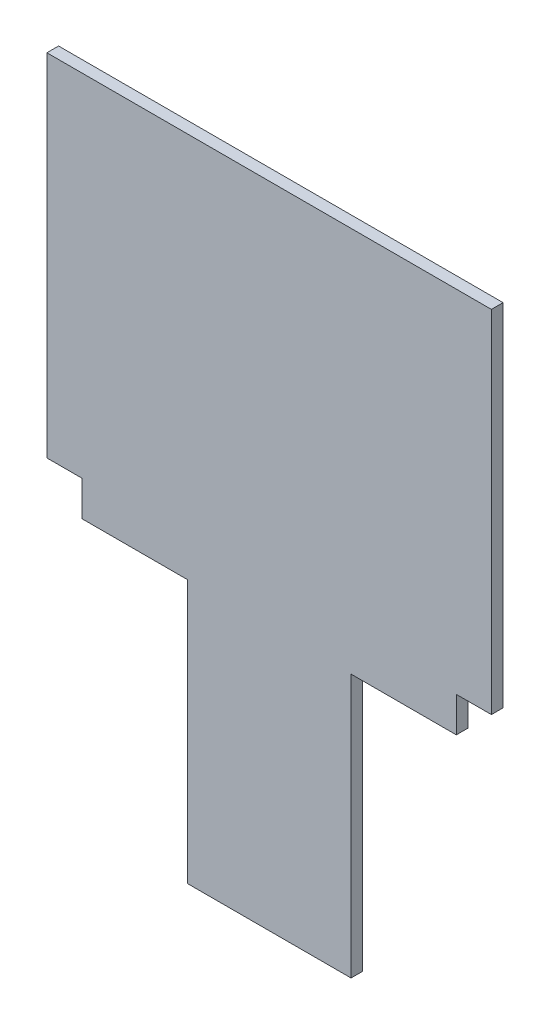
SolidWorks part; units mm, degrees
ref_plane "Ebene vorne" through (0, 0, 0) normal (0, 0, 1) x (1, 0, 0)
ref_plane "Ebene oben" through (0, 0, 0) normal (0, 1, 0) x (1, 0, 0)
ref_plane "Ebene rechts" through (0, 0, 0) normal (1, 0, 0) x (0, 0, -1)
sketch "Skizze1" plane through (0, 0, 0) normal (0, 0, 1) x (1, 0, 0)
  line L0 (14, -113) -> (14, -68) construction
  line L1 (14, -113) -> (-14, -113) construction
  line L2 (-14, -68) -> (-14, -113) construction
  line L3 (-38, -2) -> (-38, -62) construction
  line L4 (-32, -62) -> (-38, -62) construction
  line L5 (-32, -68) -> (-32, -62) construction
  line L6 (-32, -68) -> (-14, -68) construction
  line L7 (14, -68) -> (32, -68) construction
  line L8 (38, -62) -> (32, -62) construction
  line L9 (38, -62) -> (38, -2) construction
  line L10 (38, -2) -> (-38, -2) construction
  line L11 (14, -113) -> (14, -68)
  line L12 (14, -113) -> (-14, -113)
  line L13 (-14, -68) -> (-14, -113)
  line L14 (-38, -2) -> (-38, -62)
  line L15 (-32, -62) -> (-38, -62)
  line L16 (-32, -68) -> (-32, -62)
  line L17 (-32, -68) -> (-14, -68)
  line L18 (14, -68) -> (32, -68)
  line L19 (38, -62) -> (32, -62)
  line L20 (38, -62) -> (38, -2)
  line L21 (38, -2) -> (-38, -2)
  line L22 (32, -62) -> (32, -68) construction
  line L23 (32, -62) -> (32, -68)
extrude "Aufsatz-Linear austragen1" add sketch "Skizze1" against normal blind 2
